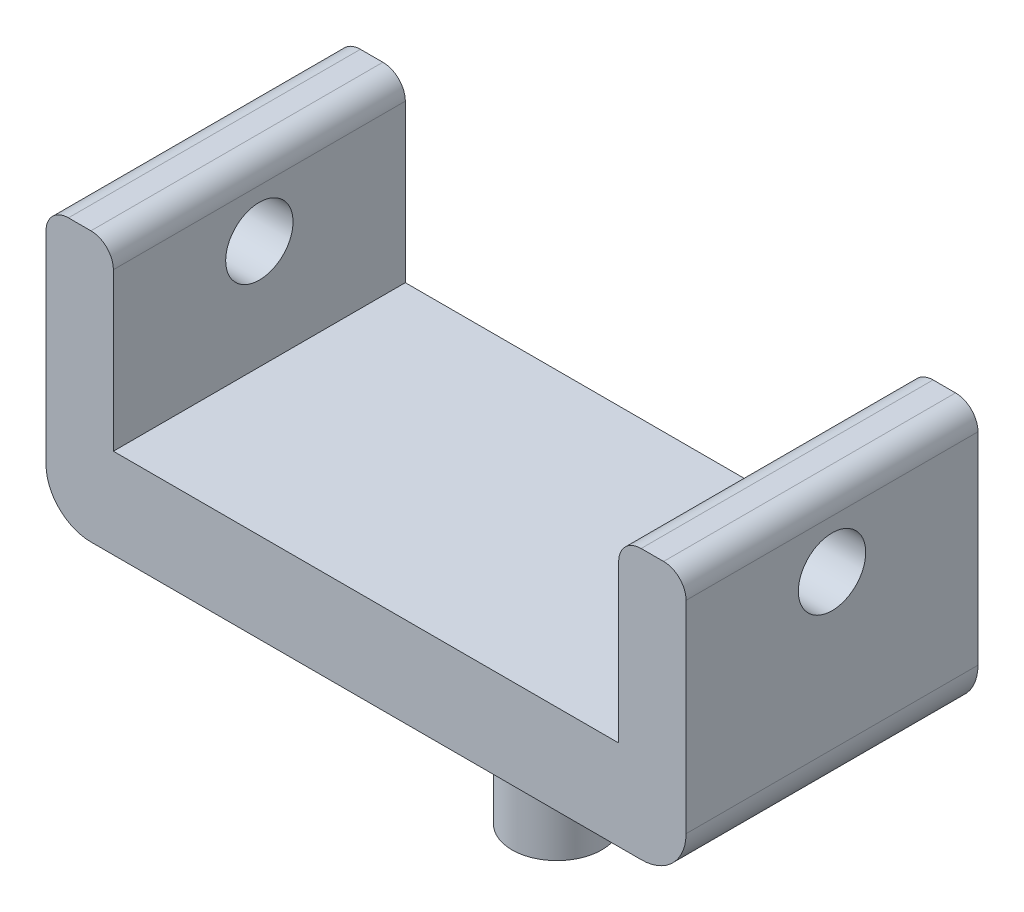
SolidWorks part; units mm, degrees
ref_plane "Front Plane" through (0, 0, 0) normal (0, 0, 1) x (1, 0, 0)
ref_plane "Top Plane" through (0, 0, 0) normal (0, 1, 0) x (1, 0, 0)
ref_plane "Right Plane" through (0, 0, 0) normal (1, 0, 0) x (0, 0, -1)
sketch "Sketch1" plane through (0, 0, 0) normal (0, 1, 0) x (1, 0, 0)
  line L1 (-12.6472, 4.8412) -> (15.8528, 4.8412)
  line L2 (-12.6472, 4.8412) -> (-12.6472, -12.1588)
  line L3 (-12.6472, -12.1588) -> (15.8528, -12.1588)
  line L4 (15.8528, 4.8412) -> (15.8528, -12.1588)
  dimension "D1" = 28.5
  dimension "D2" = 17
extrude "Boss-Extrude1" add sketch "Sketch1" along normal blind 4 contours L1 L4 L3 L2
sketch "Sketch2" plane through (0, 4, 0) normal (0, 1, 0) x (1, 0, 0)
  line L0 (-12.6472, -12.1588) -> (15.8528, -12.1588) construction
  line L1 (-12.6472, 4.8412) -> (-9.6472, 4.8412)
  line L2 (-12.6472, 4.8412) -> (-12.6472, -12.1588)
  line L3 (-12.6472, -12.1588) -> (-9.6472, -12.1588)
  line L4 (-9.6472, 4.8412) -> (-9.6472, -12.1588)
  line L6 (15.8528, 4.8412) -> (12.8528, 4.8412)
  line L7 (15.8528, 4.8412) -> (15.8528, -12.1588)
  line L8 (15.8528, -12.1588) -> (12.8528, -12.1588)
  line L9 (12.8528, 4.8412) -> (12.8528, -12.1588)
  dimension "D1" = 3
  dimension "D2" = 3
extrude "Boss-Extrude2" add sketch "Sketch2" along normal blind 8
sketch "Sketch3" plane through (-12.6472, 0, 0) normal (-1, 0, 0) x (0, 0, 1)
  line L0 (5.6588, 8.85) -> (5.6588, 12) construction
  line L1 (-4.8412, 12) -> (12.1588, 12) construction
  line L2 (12.1588, 12) -> (12.1588, 0) construction
  circle A0 centre (5.6588, 8.85) radius 1.5
  dimension "D1" = 3
  dimension "D2" = 3.15
  dimension "D3" = 6.5
extrude "Cut-Extrude1" cut sketch "Sketch3" against normal through all
sketch "Sketch4" plane through (0, 0, 0) normal (0, -1, 0) x (1, 0, 0)
  line L0 (1.6028, 12.1588) -> (1.6028, 0.9706) construction
  line L1 (-12.6472, 12.1588) -> (15.8528, 12.1588) construction
  line L2 (15.8528, 3.6588) -> (-12.6472, 3.6588) construction
  line L3 (15.8528, -4.8412) -> (15.8528, 12.1588) construction
  line L4 (-12.6472, -4.8412) -> (-12.6472, 12.1588) construction
  circle A0 centre (1.6028, 3.6588) radius 2
  dimension "D1" = 4
extrude "Boss-Extrude3" add sketch "Sketch4" along normal blind 9 contours A0
fillet "Fillet1" radius 2 1 edges at (1.6028, 0, 5.6588)
fillet "Fillet2" radius 2 2 edges at (-12.6472, 0, 3.6588) (15.8528, 0, 3.6588)
fillet "Fillet3" radius 1 4 edges at (-12.6472, 12, 3.6588) (-9.6472, 12, 3.6588) (12.8528, 12, 3.6588) (15.8528, 12, 3.6588)
sketch "Sketch5" plane through (0, 0, 0) normal (0, -1, 0) x (1, 0, 0)
  line L0 (-10.6472, -4.8412) -> (13.8528, -4.8412) construction
  line L1 (19.4592, -7.6649) -> (-17.2578, -7.6649)
  line L2 (19.4592, -7.6649) -> (19.4592, -0.8412)
  line L3 (19.4592, -0.8412) -> (-17.2578, -0.8412)
  line L4 (-17.2578, -7.6649) -> (-17.2578, -0.8412)
  dimension "D1" = 4
extrude "Cut-Extrude2" cut sketch "Sketch5" against normal up to surface (12 mm away) up to face at (14.3528, 12, 3.6588)
